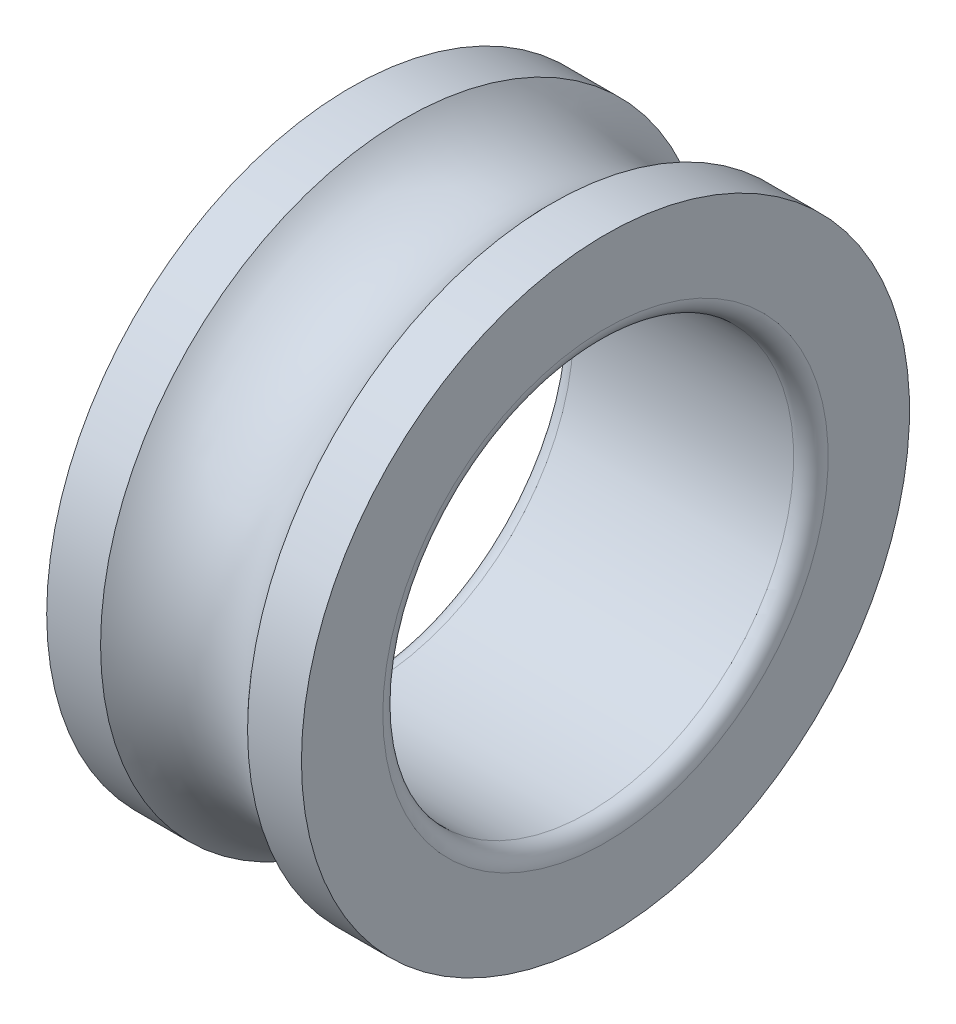
SolidWorks part; units mm, degrees
ref_plane "Front Plane" through (0, 0, 0) normal (0, 0, 1) x (1, 0, 0)
ref_plane "Top Plane" through (0, 0, 0) normal (0, 1, 0) x (1, 0, 0)
ref_plane "Right Plane" through (0, 0, 0) normal (1, 0, 0) x (0, 0, -1)
sketch "Sketch1" plane through (0, 0, 0) normal (0, 0, 1) x (1, 0, 0)
  line L0 (-24.4737, 0) -> (25.6158, 0) construction
  line L1 (0, 25) -> (0, 0) construction
  line L2 (-13.4, 25) -> (13.4, 25)
  line L3 (-15.5, 27.1) -> (-15.5, 37)
  line L4 (-15.5, 37) -> (-8.9443, 37)
  line L5 (15.5, 27.1) -> (15.5, 37)
  line L6 (-15.5, 25) -> (15.5, 37) construction
  line L7 (-15.5, 37) -> (15.5, 25) construction
  line L8 (8.9443, 37) -> (15.5, 37)
  arc A0 (-8.9443, 37) -> (8.9443, 37) centre (0, 45) ccw
  arc A1 (13.4, 25) -> (15.5, 27.1) centre (13.4, 27.1) ccw
  arc A2 (-13.4, 25) -> (-15.5, 27.1) centre (-13.4, 27.1) cw
  point P3 (0, 31)
  dimension "D5" = 12
  dimension "D6" = 2.1
  dimension "D1" = 31
  dimension "D2" = 25
  dimension "D3" = 37
  dimension "D4" = 8
revolve "Revolve1" add sketch "Sketch1" angle 360 about L0
scale "Scale1" scale about centroid uniform scaling yes scale factor 1.2
scale "Scale2" scale about centroid uniform scaling yes scale factor 0.1
